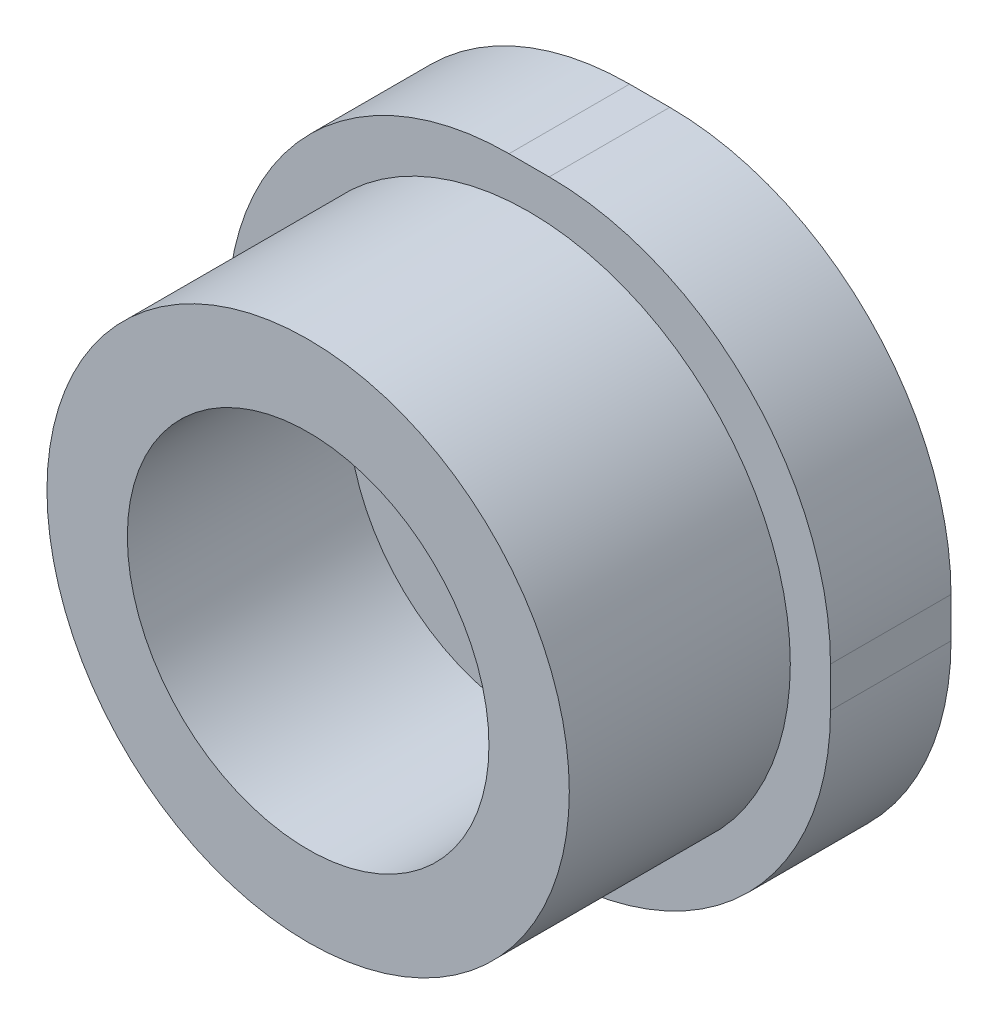
SolidWorks part; units mm, degrees
ref_plane "Front Plane" through (0, 0, 0) normal (0, 0, 1) x (1, 0, 0)
ref_plane "Top Plane" through (0, 0, 0) normal (0, 1, 0) x (1, 0, 0)
ref_plane "Right Plane" through (0, 0, 0) normal (1, 0, 0) x (0, 0, -1)
sketch "Sketch1" plane through (0, 0, 0) normal (0, 0, 1) x (1, 0, 0)
  circle A0 centre (0, 0) radius 45
  circle A1 centre (0, 0) radius 65
  dimension "D1" = 90
  dimension "D2" = 130
extrude "Boss-Extrude1" add sketch "Sketch1" along normal blind 55
sketch "Sketch2" plane through (0, 0, 0) normal (0, 0, -1) x (-1, 0, 0)
  line L1 (-5, -75) -> (5, -75)
  line L2 (-75, -5) -> (-75, 5)
  line L3 (-5, 75) -> (5, 75)
  line L4 (75, -5) -> (75, 5)
  line L5 (-75, -75) -> (75, 75) construction
  line L6 (-75, 75) -> (75, -75) construction
  arc A0 (-5, -75) -> (-75, -5) centre (-5, -5) cw
  arc A1 (5, -75) -> (75, -5) centre (5, -5) ccw
  arc A2 (5, 75) -> (75, 5) centre (5, 5) cw
  arc A3 (-75, 5) -> (-5, 75) centre (-5, 5) cw
  point P0 (0, 0)
  dimension "D3" = 70
  dimension "D1" = 150
  dimension "D2" = 150
extrude "Boss-Extrude2" add sketch "Sketch2" along normal blind 30
